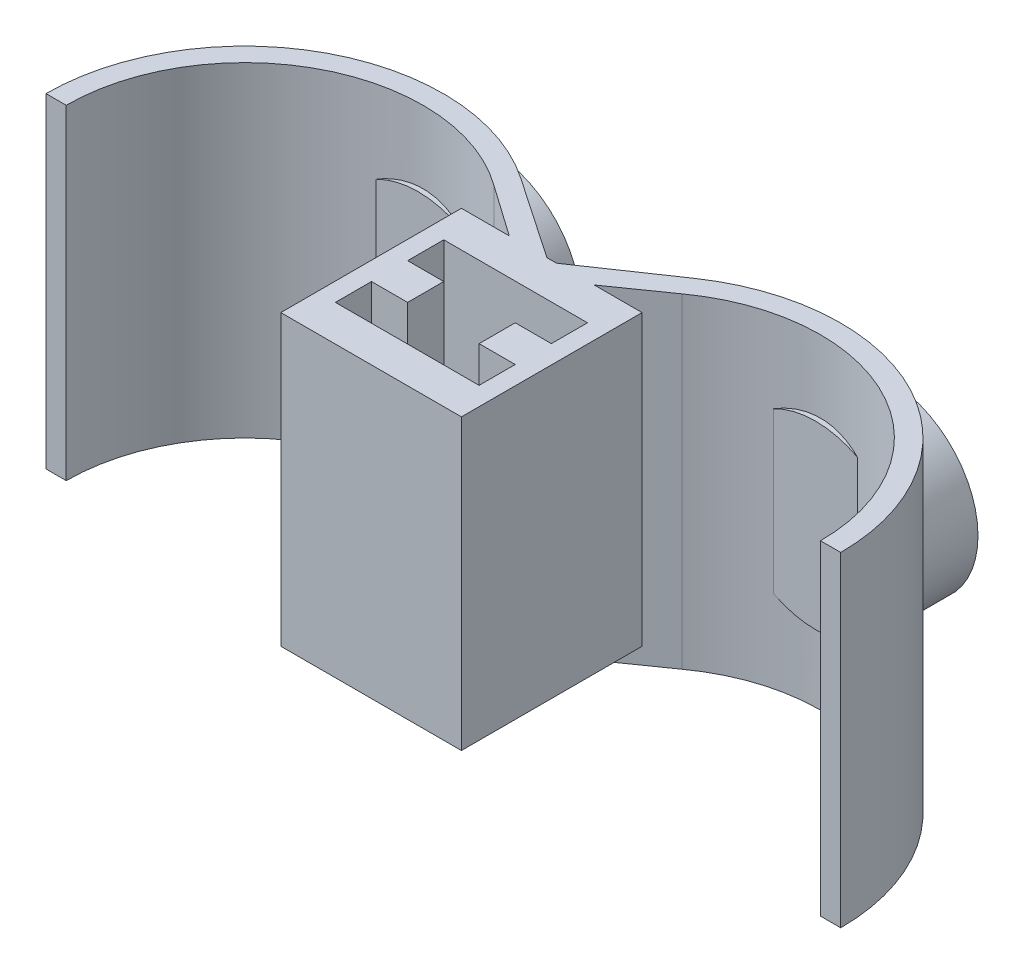
SolidWorks part; units mm, degrees
ref_plane "Front Plane" through (0, 0, 0) normal (0, 0, 1) x (1, 0, 0)
ref_plane "Top Plane" through (0, 0, 0) normal (0, 1, 0) x (1, 0, 0)
ref_plane "Right Plane" through (0, 0, 0) normal (1, 0, 0) x (0, 0, -1)
sketch "Sketch1" plane through (0, 0, 0) normal (0, 1, 0) x (1, 0, 0)
  line L0 (-55, 0) -> (55, 0) construction
  line L1 (27.5, 27.0739) -> (27.5, -27.0739) construction
  line L2 (0, 47.9889) -> (0, -47.9889) construction
  line L3 (-27.5, 27.0739) -> (-27.5, -27.0739) construction
  line L4 (-55, 0) -> (-52.2, 0)
  line L5 (52.2, 0) -> (55, 0)
  line L6 (-2.8, 0) -> (2.8, 0)
  line L7 (-12.9351, 16.36) -> (12.9351, 16.36) construction
  line L8 (-0.8442, 15.1201) -> (-12.0231, 22.7314)
  line L9 (-2.3571, 12.5286) -> (-13.5989, 20.4169)
  line L10 (2.3571, 12.5286) -> (13.5989, 20.4169)
  line L11 (0.8442, 15.1201) -> (12.0231, 22.7314)
  circle A0 centre (-27.5, 0) radius 27.5
  circle A1 centre (-27.5, 0) radius 24.7
  circle A2 centre (27.5, 0) radius 27.5
  circle A3 centre (27.5, 0) radius 24.7
  circle A4 centre (0, 16.36) radius 4.4984
  circle A5 centre (0, 16.36) radius 1.5
  point P4 (0, 0)
  point P8 (27.5, 0)
  point P11 (0, 0)
  point P26 (0, 16.36)
  dimension "D3" = 2.8
  dimension "D4" = 55
  dimension "D5" = 16.36
  dimension "D6" = 3
  dimension "D1" = 110
  dimension "D2" = 27.5
extrude "Boss-Extrude2" add sketch "Sketch1" along normal blind 45 contours A4 A0 L9 | A4 L8 A0 | A5 L8 A4 L9 L10 L11 | A4 A2 L11 | A4 L10 A2 | L10 A3 L5 A2 | A1 L9 A0 L4
sketch "Sketch2" plane through (0, 0, 0) normal (0, 0, 1) x (1, 0, 0)
  line L0 (0, 50.2649) -> (0, -50.2649) construction
  line L1 (109.3157, 22.5) -> (-109.3157, 22.5) construction
  line L2 (-0.8442, 45) -> (-12.0231, 45) construction
  line L3 (-27.5, 69.5397) -> (-27.5, -24.5397) construction
  circle A0 centre (-27.5, 22.5) radius 12.5
  circle A1 centre (27.5, 22.5) radius 12.5
  point P4 (0, 0)
  point P8 (0, 22.5)
  point P13 (-27.5, 22.5)
  dimension "D3" = 25
  dimension "D1" = 22.5
  dimension "D2" = 27.5
extrude "Boss-Extrude4" add sketch "Sketch2" against normal blind 10 from offset 24 offset against normal yes
sketch "Sketch3" plane through (0, 0, 0) normal (0, 0, 1) x (1, 0, 0)
  line L0 (0, -58.2393) -> (0, 58.2393) construction
  line L1 (-70.7674, 0) -> (70.7674, 0) construction
  line L2 (-12.5, 45) -> (12.5, 45)
  line L3 (-12.5, 45) -> (-12.5, 5)
  line L4 (-12.5, 5) -> (12.5, 5)
  line L5 (12.5, 45) -> (12.5, 5)
  line L6 (-12.5, 45) -> (12.5, 5) construction
  line L7 (-12.5, 5) -> (12.5, 45) construction
  line L8 (2.3571, 45) -> (13.0288, 45) construction
  point P0 (0, 25)
  point P4 (0, 0)
  point P13 (0, 0)
  dimension "D1" = 40
  dimension "D2" = 0
  dimension "D3" = 25
extrude "Boss-Extrude6" add sketch "Sketch3" against normal blind 25 from offset 10
sketch "Sketch5" plane through (0, 0, 0) normal (0, 1, 0) x (1, 0, 0)
  line L0 (0, -27.8838) -> (0, 27.8838) construction
  line L1 (-9.946, 10) -> (9.946, 10)
  line L2 (9.946, 10) -> (9.946, 5)
  line L3 (9.946, 5) -> (4.946, 5)
  line L4 (4.946, 5) -> (4.946, 0)
  line L5 (4.946, 0) -> (9.946, 0)
  line L6 (9.946, 0) -> (9.946, -5)
  line L7 (9.946, -5) -> (-9.946, -5)
  line L8 (12.5, 15) -> (5.8792, 15) construction
  line L9 (-9.946, 0) -> (-9.946, -5)
  line L10 (-4.946, 5) -> (-4.946, 0)
  line L11 (-4.946, 0) -> (-9.946, 0)
  line L12 (-9.946, 5) -> (-4.946, 5)
  line L13 (-9.946, 10) -> (-9.946, 5)
  point P4 (0, 0)
  point P16 (0, -5)
  point P20 (0, 10)
  dimension "D1" = 5
  dimension "D2" = 5
  dimension "D3" = 5
  dimension "D4" = 5
  dimension "D5" = 5
  dimension "D6" = 5
extrude "Cut-Extrude1" cut sketch "Sketch5" against normal blind 20 and the other way through all contours L9 L7 L6 L5 L4 L3 L2 L1 L13 L12 L10 L11
